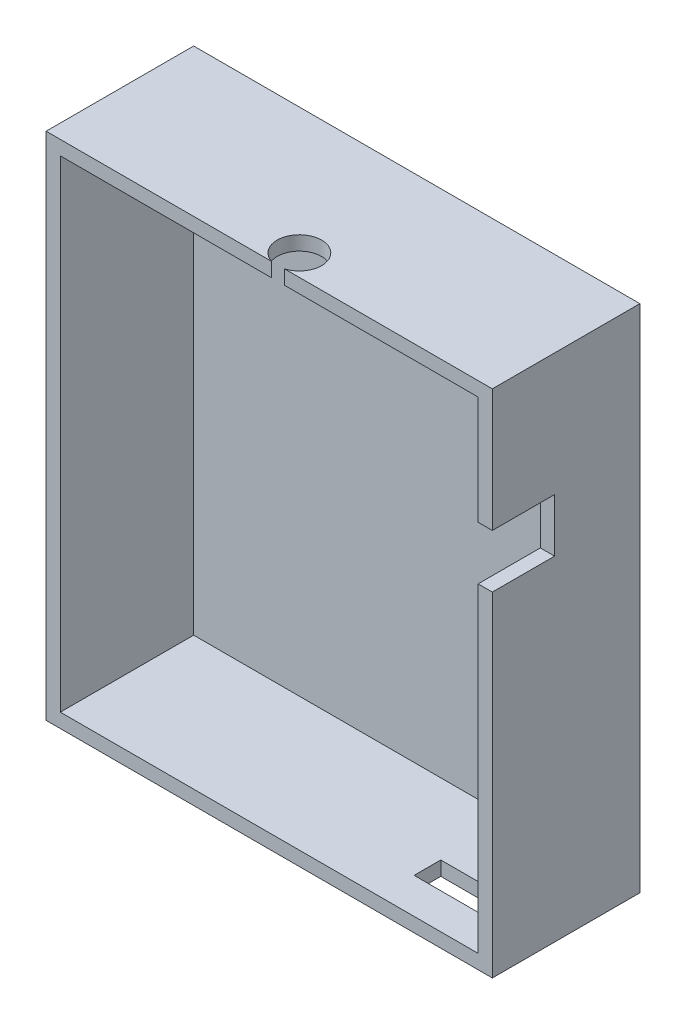
SolidWorks part; units mm, degrees
ref_plane "Płaszczyzna przednia" through (0, 0, 0) normal (0, 0, 1) x (1, 0, 0)
ref_plane "Płaszczyzna górna" through (0, 0, 0) normal (0, 1, 0) x (1, 0, 0)
ref_plane "Płaszczyzna prawa" through (0, 0, 0) normal (1, 0, 0) x (0, 0, -1)
sketch "Sketch1" plane through (0, 0, 0) normal (0, 0, 1) x (1, 0, 0)
  line L1 (0, -34.6017) -> (50.2, -34.6017)
  line L2 (0, -34.6017) -> (0, 22.7983)
  line L3 (0, 22.7983) -> (50.2, 22.7983)
  line L4 (50.2, -34.6017) -> (50.2, 22.7983)
  dimension "D1" = 50.2
  dimension "D2" = 57.4
extrude "Boss-Extrude1" add sketch "Sketch1" along normal blind 16.6
shell "Shell1" thickness 1.6
sketch "Sketch2" plane through (0, -34.6017, 0) normal (0, -1, 0) x (1, 0, 0)
  line L0 (50.2, 16.6) -> (50.2, 0) construction
  line L1 (37.4, 12.6) -> (46, 12.6)
  line L2 (37.4, 12.6) -> (37.4, 9.6)
  line L3 (37.4, 9.6) -> (46, 9.6)
  line L4 (46, 12.6) -> (46, 9.6)
  line L6 (0, 0) -> (50.2, 0) construction
  dimension "D1" = 4.2
  dimension "D2" = 8.6
  dimension "D3" = 9.6
  dimension "D4" = 3
extrude "Cut-Extrude1" cut sketch "Sketch2" against normal blind 16.6
sketch "Sketch3" plane through (50.2, 0, 0) normal (1, 0, 0) x (0, 0, -1)
  line L0 (0, -34.6017) -> (0, 22.7983) construction
  line L1 (-9.6, 2.9983) -> (-18.8, 2.9983)
  line L2 (-9.6, 2.9983) -> (-9.6, 8.9983)
  line L3 (-9.6, 8.9983) -> (-18.8, 8.9983)
  line L4 (-18.8, 2.9983) -> (-18.8, 8.9983)
  line L5 (-16.6, -34.6017) -> (0, -34.6017) construction
  dimension "D1" = 9.6
  dimension "D2" = 37.6
  dimension "D3" = 6
  dimension "D4" = 9.2
extrude "Cut-Extrude2" cut sketch "Sketch3" against normal blind 16.6
sketch "Sketch4" plane through (0, 22.7983, 0) normal (0, 1, 0) x (1, 0, 0)
  line L0 (50.2, -16.6) -> (50.2, 0) construction
  line L1 (0, -16.6) -> (0, 0) construction
  circle A0 centre (26.1, -14.2065) radius 2.5
  dimension "D1" = 24.1
  dimension "D2" = 5
  dimension "D3" = 26.1
extrude "Cut-Extrude3" cut sketch "Sketch4" against normal blind 16.6
